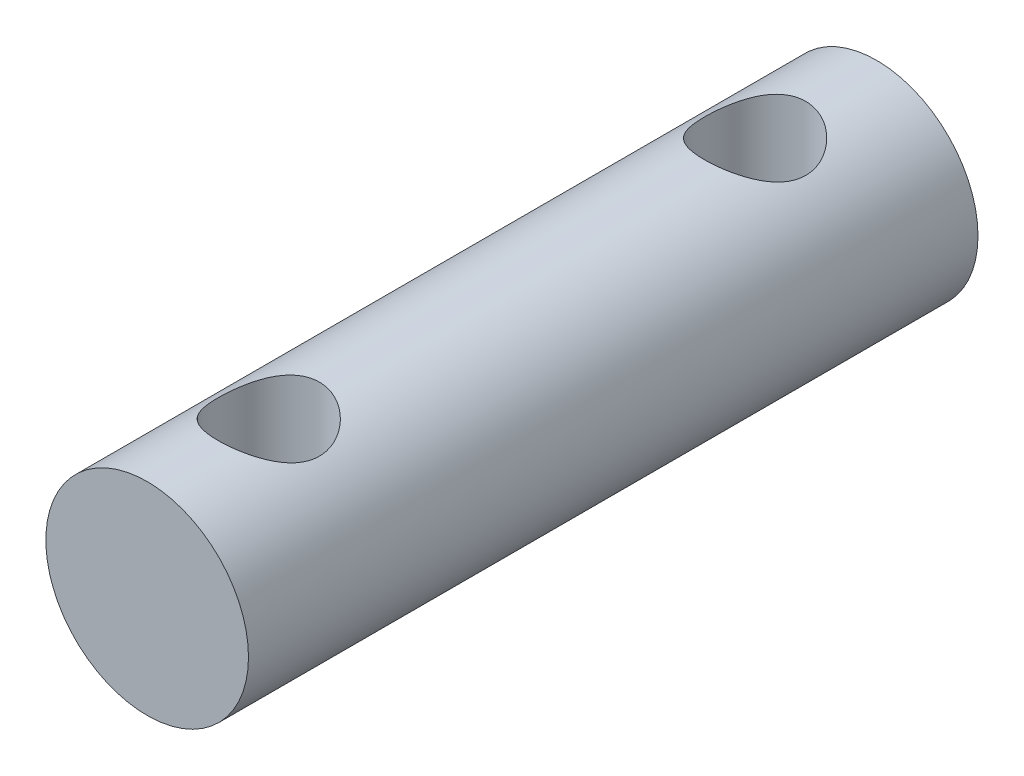
SolidWorks part; units mm, degrees
material "AISI 304"
ref_plane "Front Plane" through (0, 0, 0) normal (0, 0, 1) x (1, 0, 0)
ref_plane "Top Plane" through (0, 0, 0) normal (0, 1, 0) x (1, 0, 0)
ref_plane "Right Plane" through (0, 0, 0) normal (1, 0, 0) x (0, 0, -1)
sketch "Sketch1" plane through (0, 0, 0) normal (0, 0, 1) x (1, 0, 0)
  circle A0 centre (0, 0) radius 2.5
extrude "Boss-Extrude1" add sketch "Sketch1" along normal blind 18
sketch "Sketch2" plane through (0, 0, 0) normal (0, 1, 0) x (1, 0, 0)
  line L0 (2.5, 0) -> (-2.5, 0) construction
  circle A0 centre (0, -3) radius 1.25
  circle A1 centre (0, -15) radius 1.25
  point P6 (0, 0)
  point P7 (0, 0)
  dimension "D1" = 2.5
  dimension "D2" = 2.5
  dimension "D3" = 3
  dimension "D4" = 12
extrude "Cut-Extrude1" cut sketch "Sketch2" against normal through all both and the other way through all
